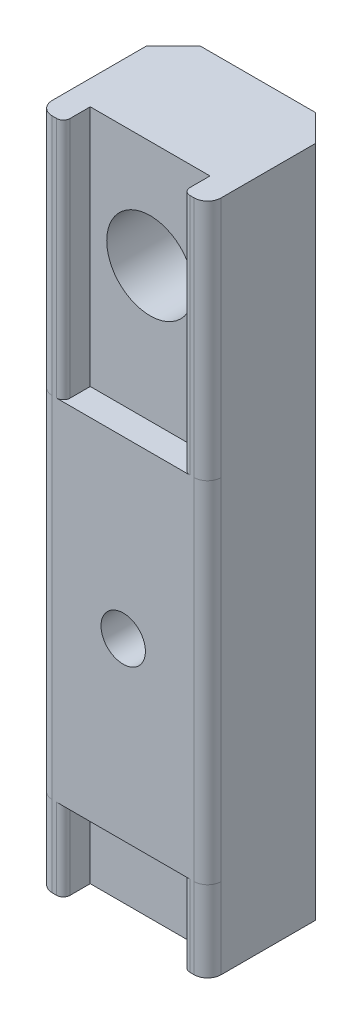
SolidWorks part; units mm, degrees
ref_plane "Front Plane" through (0, 0, 0) normal (0, 0, 1) x (1, 0, 0)
ref_plane "Top Plane" through (0, 0, 0) normal (0, 1, 0) x (1, 0, 0)
ref_plane "Right Plane" through (0, 0, 0) normal (1, 0, 0) x (0, 0, -1)
sketch "Sketch1" plane through (0, 0, 0) normal (0, 1, 0) x (1, 0, 0)
  line L0 (0, 8) -> (2, 10)
  line L1 (1, 0) -> (11.55, 0)
  line L2 (0, 1) -> (0, 8)
  line L3 (2, 10) -> (10.55, 10)
  line L4 (12.55, 1) -> (12.55, 8)
  line L5 (10.55, 10) -> (12.55, 8)
  arc A0 (11.55, 0) -> (12.55, 1) centre (11.55, 1) ccw
  arc A1 (1, 0) -> (0, 1) centre (1, 1) cw
  point P1 (12.55, 10)
  point P2 (0, 10)
  point P9 (0, 0)
  dimension "D1" = 1
  dimension "D2" = 12.55
  dimension "D3" = 9
extrude "Boss-Extrude1" add sketch "Sketch1" along normal blind 50
sketch "Sketch2" plane through (0, 0, -10) normal (0, 0, -1) x (-1, 0, 0)
  line L1 (-12.55, 25) -> (0, 25)
  line L2 (-12.55, 25) -> (-12.55, 19)
  line L3 (-12.55, 19) -> (0, 19)
  line L4 (0, 25) -> (0, 19)
  line L11 (-10.55, 50) -> (-2, 50) construction
  line L12 (-12.55, 50) -> (-12.55, 0) construction
  line L13 (0, 50) -> (0, 0) construction
  line L14 (-10.55, 25) -> (-2, 25) construction
  line L15 (-10.55, 50) -> (-10.55, 0) construction
  line L16 (-2, 50) -> (-2, 0) construction
  line L17 (-12.55, 31) -> (0, 31)
  line L18 (0, 25) -> (0, 31)
  line L19 (-12.55, 25) -> (0, 25)
  line L20 (-12.55, 25) -> (-12.55, 31)
  dimension "D2" = 25
  dimension "D3" = 6
extrude "Cut-Extrude1" [suppressed] cut sketch "Sketch2" against normal blind 2
sketch "Sketch3" plane through (0, 0, 0) normal (0, -1, 0) x (1, 0, 0)
  line L0 (1.825, 0) -> (1.825, -2)
  line L1 (1.825, -2) -> (2.825, -3)
  line L2 (6.275, 0) -> (6.275, -10) construction
  line L3 (10.55, -10) -> (2, -10) construction
  line L4 (10.725, -2) -> (10.725, 0)
  line L5 (1, 0) -> (11.55, 0) construction
  line L6 (1.825, 0) -> (10.725, 0) construction
  line L7 (1.825, 0) -> (10.725, 0)
  line L8 (10.725, -2) -> (9.725, -3)
  line L9 (9.725, -3) -> (2.825, -3)
  point P11 (6.275, 0)
  dimension "D1" = 8.9
  dimension "D2" = 1
  dimension "D3" = 1
  dimension "D4" = 3
extrude "Cut-Extrude2" cut sketch "Sketch3" against normal through all
fillet "Fillet1" radius 0.5 2 edges at (10.725, 25, 0) (1.825, 25, 0)
sketch "Sketch4" plane through (0, 0, -10) normal (0, 0, -1) x (-1, 0, 0)
  line L0 (-6.275, 50) -> (-6.275, 0) construction
  line L1 (-10.55, 0) -> (-2, 0) construction
  line L2 (-10.55, 50) -> (-2, 50) construction
  circle A0 centre (-6.275, 42) radius 3.225
  circle A1 centre (-6.275, 19) radius 1.65
  dimension "D1" = 8
  dimension "D2" = 6.45
  dimension "D3" = 3.3
  dimension "D4" = 23
extrude "Cut-Extrude3" cut sketch "Sketch4" against normal through all
sketch "Sketch5" plane through (0, 0, -3) normal (0, 0, 1) x (1, 0, 0)
  line L0 (0, 50) -> (0, 0) construction
  line L1 (0, 6) -> (12.55, 6)
  line L2 (0, 6) -> (0, 32)
  line L3 (0, 32) -> (12.55, 32)
  line L4 (12.55, 6) -> (12.55, 32)
  line L5 (12.55, 50) -> (12.55, 0) construction
  circle A0 centre (6.275, 19) radius 1.65
  point P12 (12.55, 19)
  dimension "D1" = 26
extrude "Boss-Extrude2" add sketch "Sketch5" along normal up to surface (3 mm away) up to face at (1.1625, 25, 0)
fillet "Fillet2" radius 1 2 edges at (12.55, 19, 0) (0, 19, 0)
sketch "Sketch6" plane through (0, 0, -10) normal (0, 0, -1) x (-1, 0, 0)
  line L1 (-3.013, 19) -> (-4.644, 21.825)
  line L2 (-4.644, 21.825) -> (-7.906, 21.825)
  line L3 (-7.906, 21.825) -> (-9.537, 19)
  line L4 (-9.537, 19) -> (-7.906, 16.175)
  line L5 (-7.906, 16.175) -> (-4.644, 16.175)
  line L6 (-4.644, 16.175) -> (-3.013, 19)
  circle A0 centre (-6.275, 19) radius 2.825 construction
  dimension "D1" = 5.65
extrude "Cut-Extrude4" cut sketch "Sketch6" against normal blind 4
sketch "Sketch7" plane through (0, 32, 0) normal (0, 1, 0) x (1, 0, 0)
  line L0 (1.825, 2) -> (10.725, 2)
  line L1 (10.725, 2) -> (9.725, 3)
  line L2 (9.725, 3) -> (2.825, 3)
  line L3 (2.825, 3) -> (1.825, 2)
extrude "Boss-Extrude3" add sketch "Sketch7" along normal up to surface (18 mm away) up to face at (6.275, 50, -3.0237)
sketch "Sketch8" plane through (0, 0, -3) normal (0, 0, -1) x (-1, 0, 0)
  circle A0 centre (-6.275, 42) radius 3.225
  circle A1 centre (-6.275, 42) radius 3.225 construction
extrude "Cut-Extrude5" cut sketch "Sketch8" against normal through all
sketch "Sketch9" plane through (0, 6, 0) normal (0, -1, 0) x (1, 0, 0)
  line L0 (1.825, -2) -> (10.725, -2)
  line L1 (10.725, -2) -> (9.725, -3)
  line L2 (9.725, -3) -> (2.825, -3)
  line L3 (2.825, -3) -> (1.825, -2)
extrude "Boss-Extrude4" add sketch "Sketch9" along normal up to surface (6 mm away) up to face at (6.275, 0, -3.0237)
